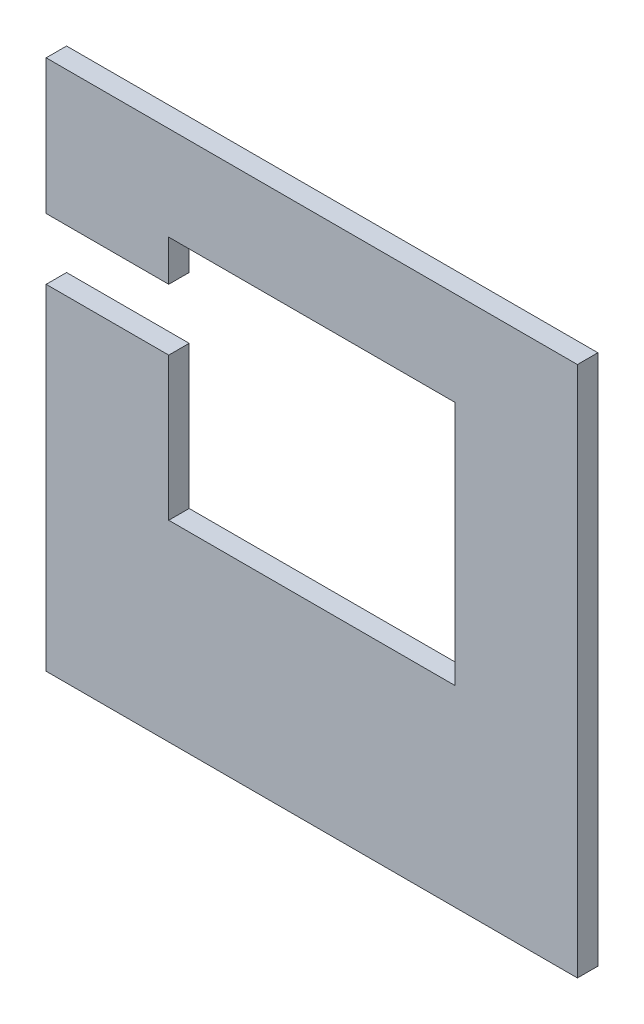
SolidWorks part; units mm, degrees
ref_plane "Piano frontale" through (0, 0, 0) normal (0, 0, 1) x (1, 0, 0)
ref_plane "Piano superiore" through (0, 0, 0) normal (0, 1, 0) x (1, 0, 0)
ref_plane "Piano destro" through (0, 0, 0) normal (1, 0, 0) x (0, 0, -1)
sketch "Schizzo1" plane through (0, 0, 0) normal (0, 0, 1) x (1, 0, 0)
  line L1 (65, -65) -> (-65, -65)
  line L2 (65, -65) -> (65, 65)
  line L3 (65, 65) -> (-65, 65)
  line L4 (-65, -65) -> (-65, 65)
  line L5 (65, -65) -> (-65, 65) construction
  line L6 (65, 65) -> (-65, -65) construction
  point P0 (0, 0)
  dimension "D1" = 130
  dimension "D2" = 130
extrude "Estrusione-Estrusione1" add sketch "Schizzo1" along normal blind 5
sketch "Schizzo2" plane through (0, 0, 5) normal (0, 0, 1) x (1, 0, 0)
  line L2 (35, -18) -> (-35, -18)
  line L3 (35, -18) -> (35, 42)
  line L4 (35, 42) -> (-35, 42)
  line L5 (-35, -18) -> (-35, 42)
  line L6 (35, -18) -> (-35, 42) construction
  line L7 (35, 42) -> (-35, -18) construction
  line L8 (65, 65) -> (-65, 65) construction
  line L10 (-65, 65) -> (-65, -65) construction
  point P2 (0, 0)
  dimension "D1" = 70
  dimension "D2" = 60
  dimension "D3" = 23
  dimension "D4" = 30
extrude "Taglio-Estrusione1" cut sketch "Schizzo2" against normal blind 5
sketch "Schizzo3" plane through (0, 0, 5) normal (0, 0, 1) x (1, 0, 0)
  line L0 (65, 65) -> (-65, 65) construction
  line L1 (-65, 32) -> (-35, 32)
  line L2 (-65, 32) -> (-65, 17)
  line L3 (-65, 17) -> (-35, 17)
  line L4 (-35, 32) -> (-35, 17)
  line L5 (-65, 32) -> (-35, 17) construction
  line L6 (-65, 17) -> (-35, 32) construction
  line L7 (-65, 65) -> (-65, -65) construction
  point P0 (-50, 24.5)
  dimension "D1" = 15
  dimension "D2" = 30
  dimension "D3" = 33
  dimension "D4" = 0
extrude "Taglio-Estrusione2" cut sketch "Schizzo3" against normal blind 10
